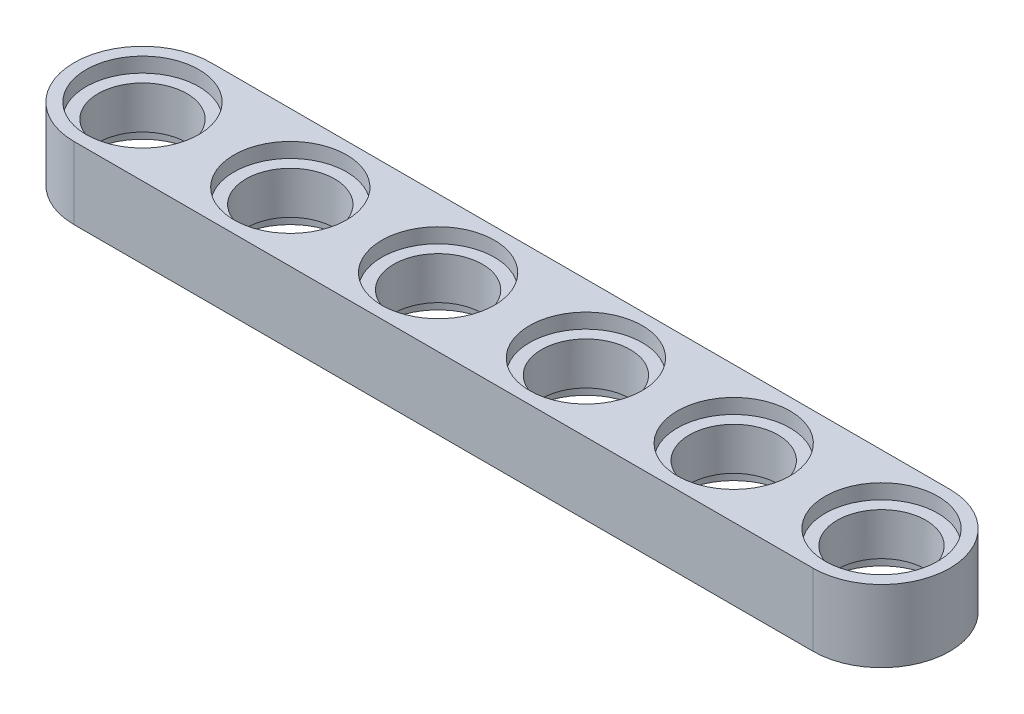
SolidWorks part; units mm, degrees
ref_plane "Front Plane" through (0, 0, 0) normal (0, 0, 1) x (1, 0, 0)
ref_plane "Top Plane" through (0, 0, 0) normal (0, 1, 0) x (1, 0, 0)
ref_plane "Right Plane" through (0, 0, 0) normal (1, 0, 0) x (0, 0, -1)
sketch "Sketch1" plane through (0, 0, 0) normal (0, 1, 0) x (1, 0, 0)
  line L0 (-16, -3.7) -> (24, -3.7)
  line L1 (-16, 3.7) -> (24, 3.7)
  arc A9 (24, 3.7) -> (24, -3.7) centre (24, 0) cw
  arc A10 (-16, 3.7) -> (-16, -3.7) centre (-16, 0) ccw
  point P20 (8, -3.7)
  point P25 (-8, -3.7)
  dimension "D1" = 3.7
  dimension "D5" = 3.7
  dimension "D2" = 40
extrude "Boss-Extrude3" add sketch "Sketch1" along normal blind 3.9 contours A10 L0 A9 L1
sketch "Sketch2" plane through (0, 3.9, 0) normal (0, 1, 0) x (1, 0, 0)
  circle A0 centre (0, 0) radius 2.4
  circle A2 centre (8, 0) radius 2.4
  circle A5 centre (16, 0) radius 2.4
  circle A6 centre (-16, 0) radius 2.4
  circle A9 centre (-8, 0) radius 2.4
  circle A10 centre (24, 0) radius 2.4
  dimension "D1" = 4.8
  dimension "D2" = 8
sketch "Sketch3" plane through (0, 3.9, 0) normal (0, 1, 0) x (1, 0, 0)
  circle A0 centre (0, 0) radius 3.05
  circle A1 centre (8, 0) radius 3.05
  circle A2 centre (16, 0) radius 3.05
  circle A3 centre (-16, 0) radius 3.05
  circle A4 centre (-8, 0) radius 3.05
  circle A6 centre (24, 0) radius 3.05
  dimension "D1" = 6.1
  dimension "D2" = 8
sketch "Sketch4" plane through (0, 0, 0) normal (0, -1, 0) x (1, 0, 0)
  circle A0 centre (0, 0) radius 3.05
  circle A1 centre (8, 0) radius 3.05
  circle A2 centre (16, 0) radius 3.05
  circle A3 centre (-16, 0) radius 3.05
  circle A4 centre (-8, 0) radius 3.05
  circle A6 centre (24, 0) radius 3.05
  dimension "D1" = 6.1
  dimension "D2" = 8
extrude "Cut-Extrude1" cut sketch "Sketch2" against normal blind 7.8
extrude "Cut-Extrude2" cut sketch "Sketch3" against normal blind 0.8
extrude "Cut-Extrude3" cut sketch "Sketch4" against normal blind 0.8
